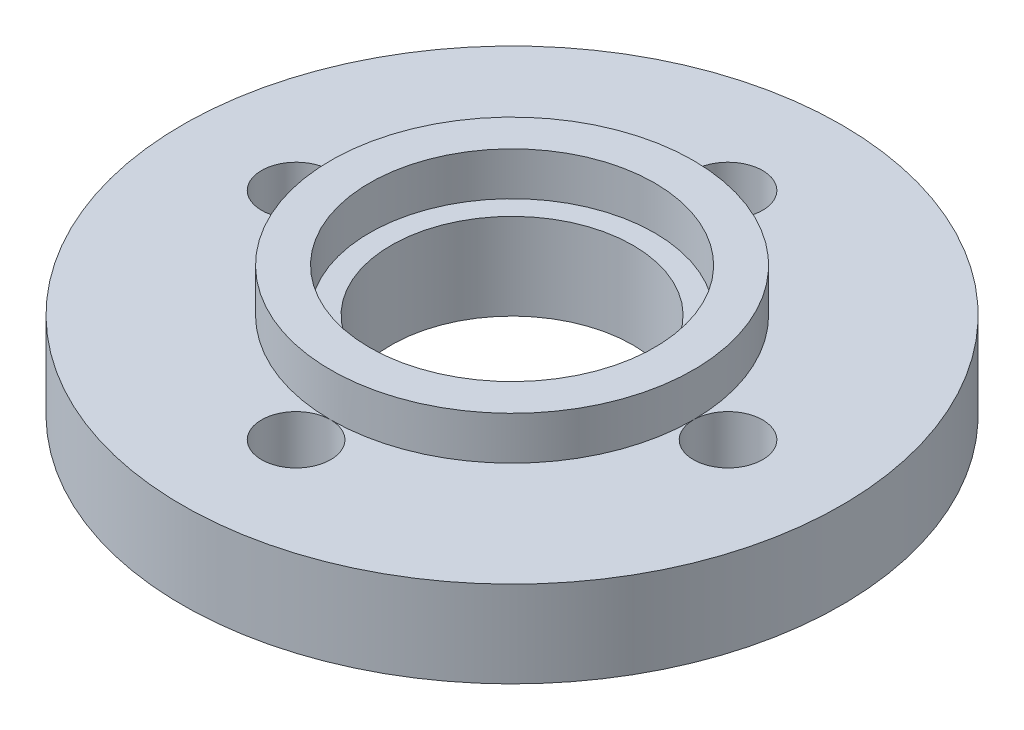
SolidWorks part; units mm, degrees
ref_plane "Спереди" through (0, 0, 0) normal (0, 0, 1) x (1, 0, 0)
ref_plane "Сверху" through (0, 0, 0) normal (0, 1, 0) x (1, 0, 0)
ref_plane "Справа" through (0, 0, 0) normal (1, 0, 0) x (0, 0, -1)
other "Configuration Table"
sketch "Sketch1" plane through (0, 0, 0) normal (0, 0, 1) x (1, 0, 0)
  line L0 (14, 0.2336) -> (38.1501, 0.2336)
  line L1 (38.1501, 0.2336) -> (38.1501, 10.2336)
  line L2 (38.1501, 10.2336) -> (21, 10.2336)
  line L3 (21, 10.2336) -> (21, 15.2336)
  line L4 (21, 15.2336) -> (16.5, 15.2336)
  line L5 (16.5, 15.2336) -> (16.5, 10.2336)
  line L6 (16.5, 10.2336) -> (14, 10.2336)
  line L7 (14, 10.2336) -> (14, 0.2336)
  line L8 (0, 0) -> (0, 36.6782) construction
  line L9 (-14, 10.2336) -> (-14, 0.2336)
  line L10 (-16.5, 10.2336) -> (-14, 10.2336)
  line L11 (-16.5, 15.2336) -> (-16.5, 10.2336)
  line L12 (-21, 15.2336) -> (-16.5, 15.2336)
  line L13 (-21, 10.2336) -> (-21, 15.2336)
  line L14 (-38.1501, 10.2336) -> (-21, 10.2336)
  line L15 (-38.1501, 0.2336) -> (-38.1501, 10.2336)
  line L16 (-14, 0.2336) -> (-38.1501, 0.2336)
  point P19 (21, 12.7336)
  dimension "D1" = 15
  dimension "D2" = 5
  dimension "D4" = 42
  dimension "D5" = 33
  dimension "D6" = 28
sketch "Sketch7" plane through (0, 0, 0) normal (0, 0, 1) x (1, 0, 0)
revolve "Revolve2" add sketch "Sketch1" angle 360 about L8
sketch "Sketch14" plane through (0, 10.2336, 0) normal (0, 1, 0) x (1, 0, 0)
  line L1 (-50, 0) -> (50, 0) construction
  circle A0 centre (25, 0) radius 4
  circle A1 centre (0, 25) radius 4
  circle A2 centre (0, 0) radius 25 construction
  circle A3 centre (-25, 0) radius 4
  circle A4 centre (0, -25) radius 4
  point P16 (0, 0)
  point P17 (0, 0)
  dimension "D1" = 8
  dimension "D2" = 50
  dimension "D3" = 4
extrude "Cut-Extrude2" cut sketch "Sketch14" against normal up to surface (10 mm away) up to face at (0, 0.2336, -38.1501)
